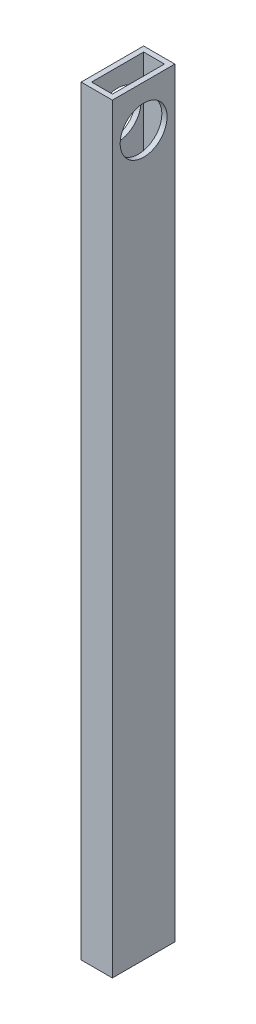
SolidWorks part; units mm, degrees
ref_plane "Front Plane" through (0, 0, 0) normal (0, 0, 1) x (1, 0, 0)
ref_plane "Top Plane" through (0, 0, 0) normal (0, 1, 0) x (1, 0, 0)
ref_plane "Right Plane" through (0, 0, 0) normal (1, 0, 0) x (0, 0, -1)
sketch "Sketch1" plane through (0, 0, 0) normal (0, 1, 0) x (1, 0, 0)
  line L1 (0, 0) -> (19.05, 0)
  line L2 (0, 0) -> (0, 38.1)
  line L3 (0, 38.1) -> (19.05, 38.1)
  line L4 (19.05, 0) -> (19.05, 38.1)
  dimension "D1" = 38.1
  dimension "D2" = 19.05
extrude "Extrude-Thin1" add sketch "Sketch1" along normal blind 463.55 thin thin type one direction reverse wall 3.175
sketch "Sketch2" plane through (19.05, 0, 0) normal (1, 0, 0) x (0, 0, -1)
  line L0 (38.1, 463.55) -> (38.1, 0) construction
  line L1 (0, 463.55) -> (38.1, 463.55) construction
  circle A0 centre (19.05, 438.15) radius 14.2875
  dimension "D1" = 28.575
  dimension "D2" = 19.05
  dimension "D3" = 25.4
extrude "Cut-Extrude1" cut sketch "Sketch2" against normal blind 19.05
